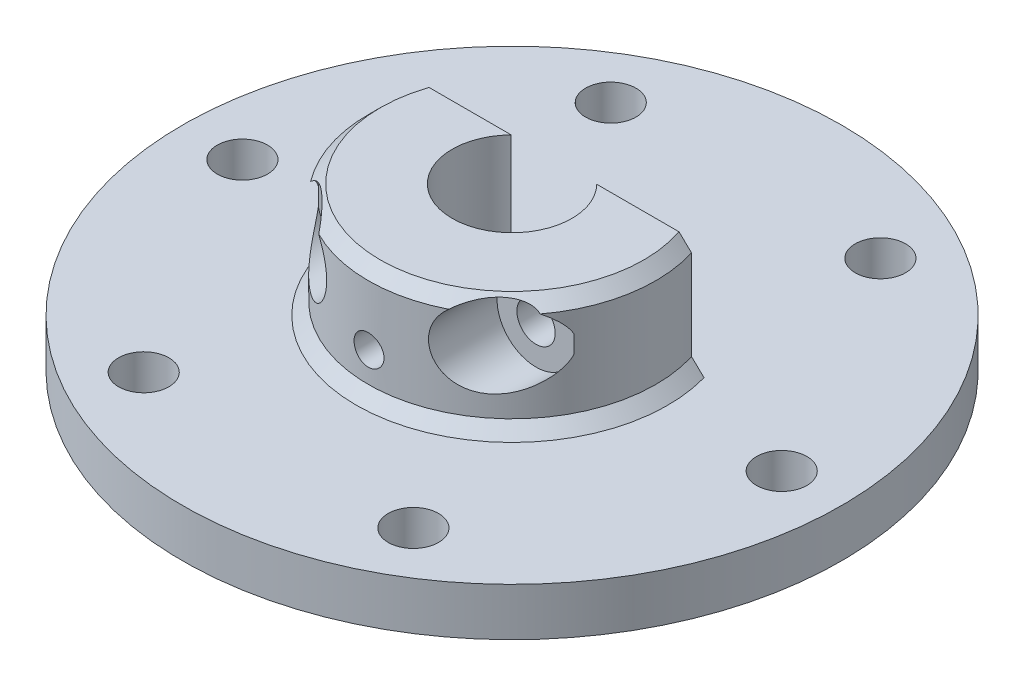
SolidWorks part; units mm, degrees
material "6061 合金"
ref_plane "前视基准面" through (0, 0, 0) normal (0, 0, 1) x (1, 0, 0)
ref_plane "上视基准面" through (0, 0, 0) normal (0, 1, 0) x (1, 0, 0)
ref_plane "右视基准面" through (0, 0, 0) normal (1, 0, 0) x (0, 0, -1)
sketch "草图1" plane through (0, 0, 0) normal (0, 0, 1) x (1, 0, 0)
  line L0 (0, 0) -> (0, 21.0564) construction
  line L1 (-10, 2) -> (-27.5, 2)
  line L2 (-27.5, 2) -> (-27.5, 6)
  line L3 (-27.5, 6) -> (-12, 6)
  line L4 (-12, 6) -> (-12, 15.5)
  line L5 (-12, 15.5) -> (-5, 15.5)
  line L8 (-5, 15.5) -> (-5, 0)
  line L9 (-10, 2) -> (-10, 0)
  line L10 (-10, 0) -> (-5, 0)
  dimension "D1" = 10
  dimension "D3" = 24
  dimension "D4" = 55
  dimension "D5" = 4
  dimension "D6" = 13.5
  dimension "D8" = 2
  dimension "D9" = 20
revolve "旋转1" add sketch "草图1" angle 360 about L0
sketch "草图2" plane through (0, 2, 0) normal (0, -1, 0) x (1, 0, 0)
  circle A0 centre (0, 0) radius 22.5 construction
  circle A1 centre (-11.25, 19.4856) radius 1
  circle A2 centre (11.25, 19.4856) radius 1
  circle A3 centre (22.5, 0) radius 1
  circle A4 centre (11.25, -19.4856) radius 1
  circle A5 centre (-11.25, -19.4856) radius 1
  circle A6 centre (-22.5, 0) radius 1
  point P18 (0, 0)
  dimension "D1" = 45
  dimension "D2" = 2
  dimension "D3" = 6
extrude "切除-拉伸2" cut sketch "草图2" against normal blind 10
sketch "草图6" plane through (0, 15.5, 0) normal (0, -1, 0) x (1, 0, 0)
  line L0 (11.4782, -3.5) -> (-11.4782, -3.5)
  circle A5 centre (0, 0) radius 12 construction
  arc A6 (-11.4782, -3.5) -> (11.4782, -3.5) centre (0, 0) ccw
  circle A7 centre (0, 0) radius 12 construction
  dimension "D2" = 3.5
extrude "切除-拉伸4" cut sketch "草图6" along normal up to surface (9.5 mm away) up to face at (-22.5, 6, -1)
chamfer "倒角1" distance 1 angle 45 2 edges at (0, 15.5, 12) (0, 6, 12)
sketch "草图3" plane through (0, 0, 0) normal (0, 0, 1) x (1, 0, 0)
  line L0 (27.5, 6) -> (-27.5, 6) construction
  line L1 (0, 12) -> (0, 0) construction
  line L2 (7.5, 12) -> (-7.5, 12) construction
  line L4 (12, 15.5) -> (-12, 15.5) construction
  circle A0 centre (0, 9.5) radius 1.25
  circle A1 centre (7.5, 12) radius 1.6
  circle A2 centre (-7.5, 12) radius 1.6
  dimension "D2" = 2.5
  dimension "D1" = 3.5
  dimension "D3" = 15
  dimension "D4" = 3.2
  dimension "D5" = 3.5
extrude "切除-拉伸3" cut sketch "草图3" against normal through all and the other way through all
cosmetic thread "装饰螺纹线1" parameters "D2"=3
ref_plane "基准面1" through (0, 0, 5.5) normal (0, 0, -1) x (-1, 0, 0)
sketch "草图7" plane through (0, 0, 5.5) normal (0, 0, -1) x (-1, 0, 0)
  circle A0 centre (-7.5, 12) radius 3.25
  circle A1 centre (7.5, 12) radius 3.25
  dimension "D1" = 6.5
extrude "切除-拉伸5" cut sketch "草图7" against normal through all
hole_wizard "M5 螺纹孔1" positions "草图8" profile "草图9" tap size "M5" standard "GB" end condition through all
sketch "草图8" plane through (0, 6, 0) normal (0, 1, 0) x (1, 0, 0)
  point P0 (11.25, 19.4856)
  point P3 (22.5, 0)
  point P6 (11.25, -19.4856)
  point P9 (-11.25, -19.4856)
  point P12 (-22.5, 0)
  point P15 (-11.25, 19.4856)
sketch "草图9" plane through (11.25, 6, -19.4856) normal (1, 0, 0) x (0, 0, 1)
  line L0 (0, 0) -> (0, 6)
  line L1 (0, 6) -> (2.1, 6)
  line L2 (2.1, 6) -> (2.1, 0)
  line L5 (2.1, 0) -> (0, 0)
  line L11 (0, -6.35) -> (0, 107.95) construction
  dimension "通孔螺纹孔钻头直径" = 4.2
  dimension "通孔螺纹孔钻头深度" = 6
cosmetic thread "孔螺蚊线1" parameters "D2"=5
cosmetic thread "孔螺蚊线2" parameters "D2"=5
cosmetic thread "孔螺蚊线3" parameters "D2"=5
cosmetic thread "孔螺蚊线4" parameters "D2"=5
cosmetic thread "孔螺蚊线5" parameters "D2"=5
cosmetic thread "孔螺蚊线6" parameters "D2"=5
